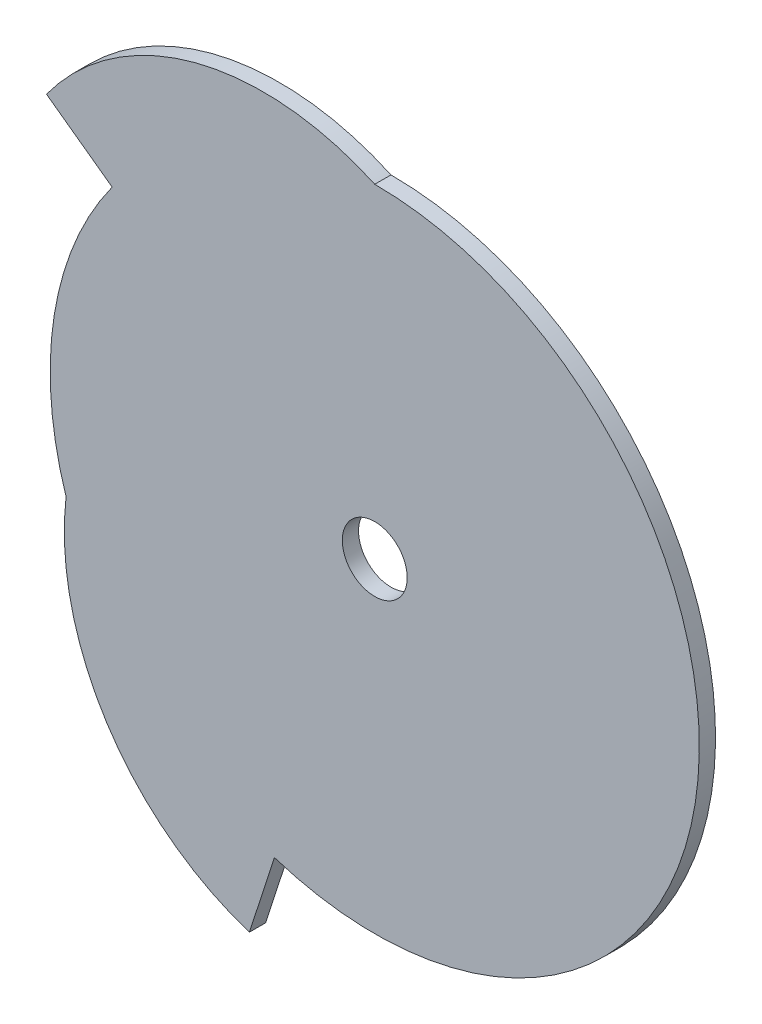
SolidWorks part; units mm, degrees
ref_plane "Alzado" through (0, 0, 0) normal (0, 0, 1) x (1, 0, 0)
ref_plane "Planta" through (0, 0, 0) normal (0, 1, 0) x (1, 0, 0)
ref_plane "Vista lateral" through (0, 0, 0) normal (1, 0, 0) x (0, 0, -1)
sketch "Croquis1" plane through (0, 0, 0) normal (0, 0, 1) x (1, 0, 0)
  line L0 (-60, 0) -> (60, 0) construction
  line L1 (0, 0) -> (-48.541, 35.2671) construction
  line L2 (-18.541, 57.0634) -> (18.541, -57.0634) construction
  line L3 (18.541, 57.0634) -> (-18.541, -57.0634) construction
  line L4 (48.541, 35.2671) -> (0, 0) construction
  line L5 (0, 0) -> (48.541, -35.2671) construction
  line L6 (-48.541, 35.2671) -> (-60.6763, 44.0839)
  line L7 (-18.541, -57.0634) -> (-23.1763, -71.3292)
  line L8 (0, 0) -> (-48.541, -35.2671) construction
  arc A0 (-18.541, -57.0634) -> (0, 60) centre (0, 0) ccw
  arc A1 (-60.6763, 44.0839) -> (-75, 0) centre (0, 0) ccw construction
  arc A3 (-23.1763, 71.3292) -> (-60.6763, 44.0839) centre (0, 0) ccw construction
  arc A4 (23.1763, 71.3292) -> (-23.1763, 71.3292) centre (0, 0) ccw construction
  arc A6 (-60.6763, -44.0839) -> (-23.1763, -71.3292) centre (0, 0) ccw construction
  arc A7 (-23.1763, -71.3292) -> (23.1763, 71.3292) centre (0, 0) ccw construction
  arc A8 (-75, 0) -> (-60.6763, -44.0839) centre (0, 0) ccw construction
  arc A9 (-60.6763, 44.0839) -> (0, 60) centre (-20.6159, 14.9783) cw
  arc A10 (-23.1763, -71.3292) -> (-57.0634, -18.541) centre (-7.8746, -24.2355) cw
  arc A11 (-48.541, -35.2671) -> (-18.541, -57.0634) centre (0, 0) ccw construction
  arc A12 (-57.0634, -18.541) -> (-48.541, -35.2671) centre (0, 0) ccw construction
  arc A13 (-18.541, 57.0634) -> (-48.541, 35.2671) centre (0, 0) ccw construction
  arc A14 (-48.541, 35.2671) -> (-57.0634, -18.541) centre (0, 0) ccw
  arc A15 (0, 60) -> (-18.541, 57.0634) centre (0, 0) ccw construction
  dimension "D6" = 120
  dimension "D7" = 75
  dimension "D1" = 36
  dimension "D2" = 36
  dimension "D3" = 36
  dimension "D4" = 36
  dimension "D5" = 36
extrude "Saliente-Extruir1" add sketch "Croquis1" along normal blind 3
sketch "Croquis2" plane through (0, 0, 3) normal (0, 0, 1) x (1, 0, 0)
  circle A0 centre (0, 0) radius 6
  dimension "D1" = 12
extrude "Cortar-Extruir1" cut sketch "Croquis2" against normal blind 3
equation "\"D6@Croquis1\"=60*2"
